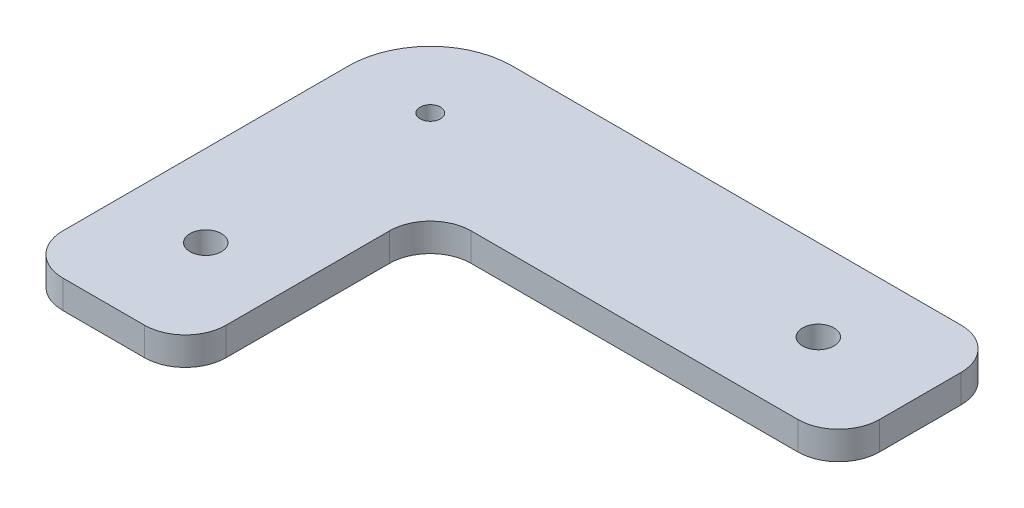
SolidWorks part; units mm, degrees
ref_plane "Front Plane" through (0, 0, 0) normal (0, 0, 1) x (1, 0, 0)
ref_plane "Top Plane" through (0, 0, 0) normal (0, 1, 0) x (1, 0, 0)
ref_plane "Right Plane" through (0, 0, 0) normal (1, 0, 0) x (0, 0, -1)
sketch "Sketch1" plane through (0, 0, 0) normal (0, 1, 0) x (1, 0, 0)
  line L0 (0, 0) -> (0, 100)
  line L1 (0, 100) -> (140, 100)
  line L2 (140, 100) -> (140, 60)
  line L3 (140, 60) -> (40, 60)
  line L4 (40, 60) -> (40, 0)
  line L5 (40, 0) -> (0, 0)
  dimension "D1" = 140
  dimension "D2" = 100
  dimension "D3" = 40
extrude "Boss-Extrude1" add sketch "Sketch1" along normal blind 6.9
fillet "Fillet1" radius 10 5 edges at (140, 3.45, -100) (140, 3.45, -60) (0, 3.45, 0) (40, 3.45, 0) (40, 3.45, -60)
fillet "Fillet2" radius 20 1 edges at (0, 3.45, -100)
sketch "Sketch3" plane through (0, 6.9, 0) normal (0, 1, 0) x (1, 0, 0)
  line L0 (0, 80) -> (0, 10) construction
  line L1 (20, 80) -> (0, 80) construction
  line L2 (20, 80) -> (20, 100) construction
  line L3 (20, 100) -> (0, 100) construction
  line L4 (0, 80) -> (0, 100) construction
  line L5 (130, 100) -> (20, 100) construction
  circle A0 centre (20, 80) radius 2.5
  dimension "D2" = 5
  dimension "D1" = 20
extrude "Cut-Extrude2" cut sketch "Sketch3" against normal through all
sketch "Sketch2" plane through (0, 6.9, 0) normal (0, 1, 0) x (1, 0, 0)
  line L0 (20, 0) -> (20, 77.5) construction
  line L1 (10, 0) -> (30, 0) construction
  line L3 (140, 70) -> (140, 90) construction
  line L4 (140, 80) -> (22.5, 80) construction
  circle A3 centre (20, 80) radius 2.5 construction
  circle A4 centre (20, 25) radius 3.85
  circle A5 centre (115, 80) radius 3.85
  point P15 (0, 0)
  dimension "D1" = 25
  dimension "D2" = 7.7
  dimension "D3" = 25
extrude "Cut-Extrude1" cut sketch "Sketch2" against normal through all
